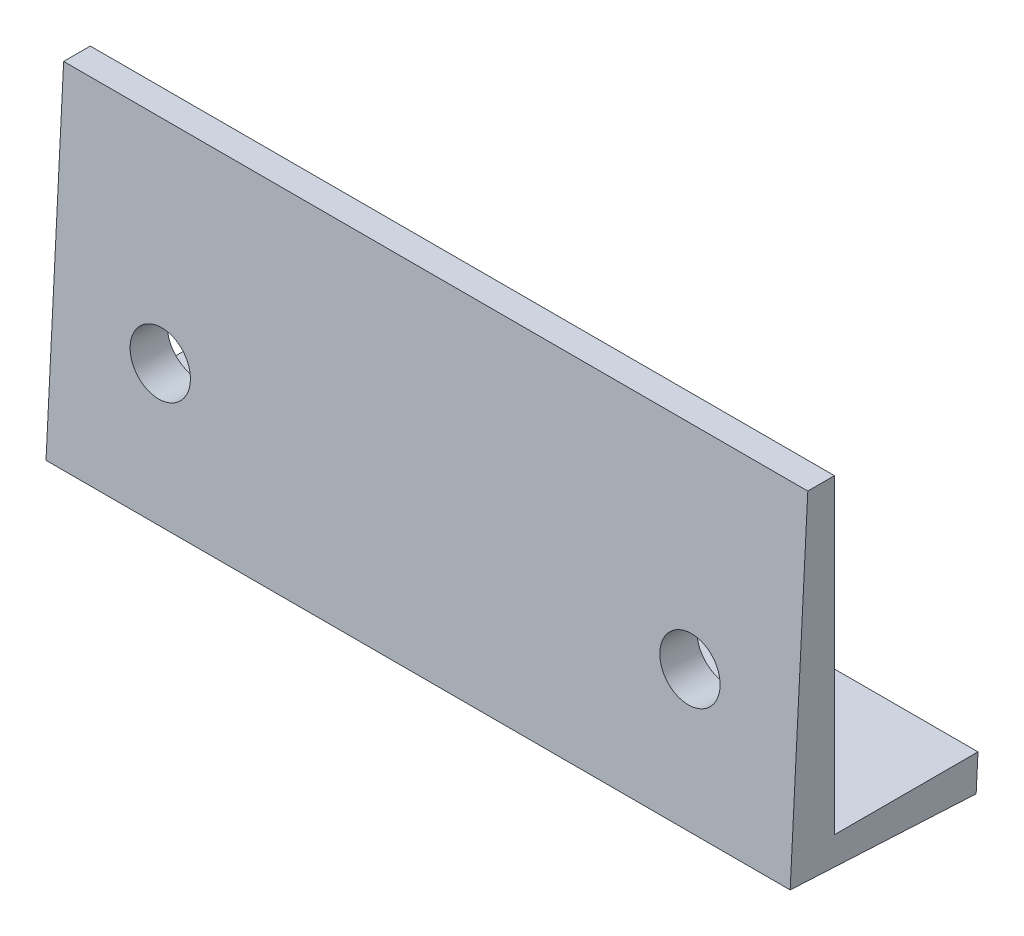
SolidWorks part; units mm, degrees
ref_plane "Top Plane" through (0, 0, 0) normal (0, 0, 1) x (1, 0, 0)
ref_plane "Front Plane" through (0, 0, 0) normal (0, 1, 0) x (1, 0, 0)
ref_plane "Right Plane" through (0, 0, 0) normal (1, 0, 0) x (0, 0, -1)
sketch "Sketch1" plane through (0, 0, 0) normal (0, 0, 1) x (1, 0, 0)
  line L1 (-42, -19) -> (42, -19)
  line L2 (-42, -19) -> (-42, 19)
  line L3 (-42, 19) -> (42, 19)
  line L4 (42, -19) -> (42, 19)
  line L5 (-42, -19) -> (42, 19) construction
  line L6 (-42, 19) -> (42, -19) construction
  point P0 (0, 0)
  dimension "D1" = 38
  dimension "D2" = 84
extrude "Boss-Extrude1" add sketch "Sketch1" along normal blind 5
sketch "Sketch2" plane through (0, 0, 5) normal (0, 0, 1) x (1, 0, 0)
  line L1 (-42, -19) -> (42, -19)
  line L2 (-42, -19) -> (-42, 23)
  line L3 (-42, 23) -> (42, 23)
  line L4 (42, -19) -> (42, 23)
  dimension "D1" = 84
  dimension "D2" = 42
revolve "Cut-Revolve1" cut sketch "Sketch2" angle 3 about L1
sketch "Sketch4" plane through (0, 0.2093, 3.9933) normal (0, 0.0523, 0.9986) x (1, 0, 0)
  circle A3 centre (29.8957, -4.0835) radius 3.4
  circle A4 centre (-29.8957, -4.0835) radius 3.4
  dimension "D1" = 6.8
  dimension "D2" = 6.8
sketch "Sketch5" plane through (0, -19, 0) normal (0, -1, 0) x (1, 0, 0)
  line L1 (-42, 0) -> (42, 0)
  line L2 (-42, 0) -> (-42, 5)
  line L3 (-42, 5) -> (42, 5)
  line L4 (42, 0) -> (42, 5)
revolve "Revolve1" add sketch "Sketch5" angle 3 about L3
sketch "Sketch6" plane through (-42, 0, 0) normal (-1, 0, 0) x (0, -1, 0)
  line L0 (19, 5) -> (19.2617, 0.0069) construction
  line L1 (19.2617, 0.0069) -> (20.1002, -15.9931)
  line L2 (20.1002, -15.9931) -> (16.1002, -16.2028)
  line L3 (16.1002, -16.2028) -> (16.1002, 0)
  line L4 (-19, 0) -> (19, 0) construction
  line L5 (16.1002, 0) -> (19.2617, 0.0069)
  dimension "D1" = 16
  dimension "D2" = 4
extrude "Boss-Extrude3" add sketch "Sketch6" against normal up to vertex (84 mm away)
extrude "Cut-Extrude1" cut sketch "Sketch4" against normal blind 10
